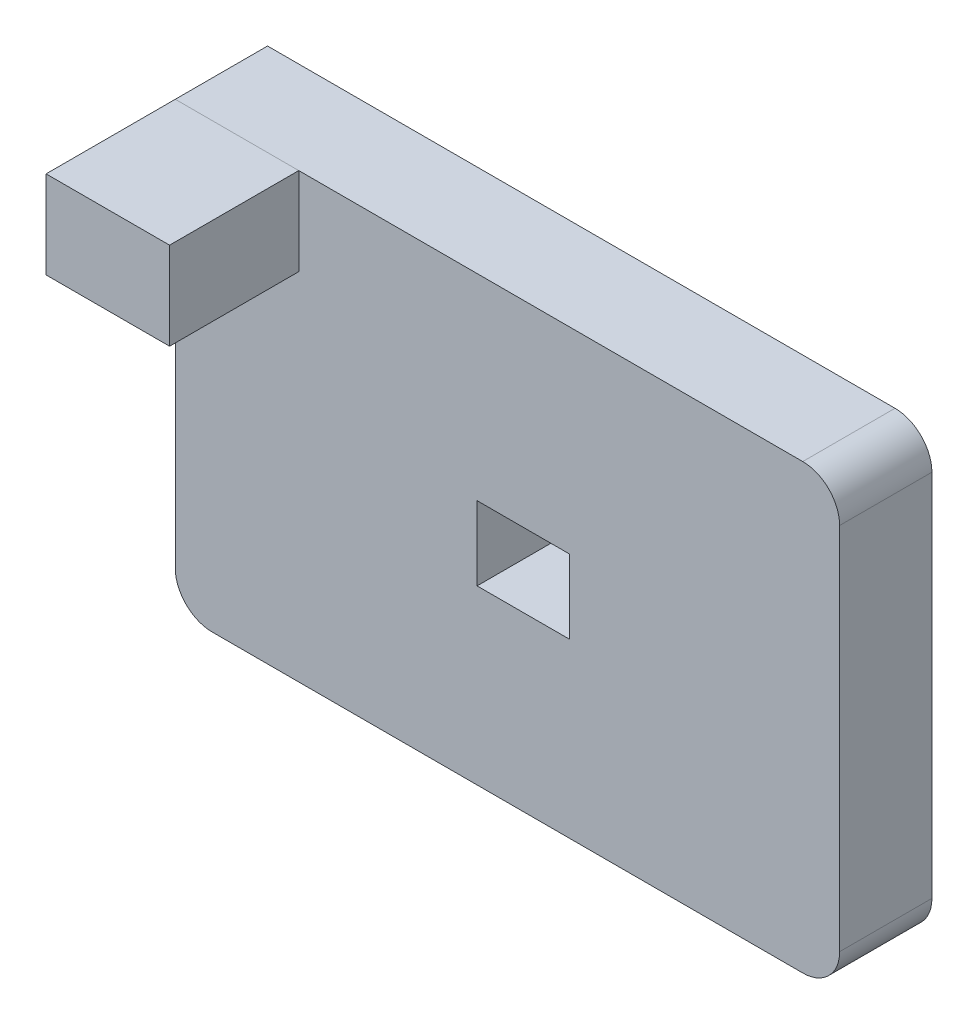
SolidWorks part; units mm, degrees
ref_plane "Front Plane" through (0, 0, 0) normal (0, 0, 1) x (1, 0, 0)
ref_plane "Top Plane" through (0, 0, 0) normal (0, 1, 0) x (1, 0, 0)
ref_plane "Right Plane" through (0, 0, 0) normal (1, 0, 0) x (0, 0, -1)
sketch "Sketch1" plane through (0, 0, 0) normal (0, 0, 1) x (1, 0, 0)
  line L1 (0, 0) -> (180, 0)
  line L2 (0, 0) -> (0, 120)
  line L3 (0, 120) -> (180, 120)
  line L4 (180, 0) -> (180, 120)
  line L6 (81.7731, 66.7108) -> (106.7731, 66.7108)
  line L7 (81.7731, 66.7108) -> (81.7731, 46.7108)
  line L8 (81.7731, 46.7108) -> (106.7731, 46.7108)
  line L9 (106.7731, 66.7108) -> (106.7731, 46.7108)
  line L10 (81.7731, 66.7108) -> (106.7731, 46.7108) construction
  line L11 (81.7731, 46.7108) -> (106.7731, 66.7108) construction
  point P7 (94.2731, 56.7108)
  dimension "D1" = 180
  dimension "D2" = 120
  dimension "D3" = 20
  dimension "D4" = 25
  dimension "D5" = 56.7108
  dimension "D6" = 81.7731
extrude "Boss-Extrude1" add sketch "Sketch1" along normal blind 25 contours L2 L1 L4 L3 | L7 L6 L9 L8
sketch "Sketch2" plane through (0, 0, 25) normal (0, 0, 1) x (1, 0, 0)
  line L1 (0, 120) -> (33.4578, 120)
  line L2 (0, 120) -> (0, 96.2812)
  line L3 (0, 96.2812) -> (33.4578, 96.2812)
  line L4 (33.4578, 120) -> (33.4578, 96.2812)
  dimension "D1" = 33.4578
  dimension "D2" = 23.7188
extrude "Boss-Extrude2" add sketch "Sketch2" along normal blind 35 separate body
fillet "Fillet1" radius 10 3 edges at (180, 120, 12.5) (180, 0, 12.5) (0, 0, 12.5)
